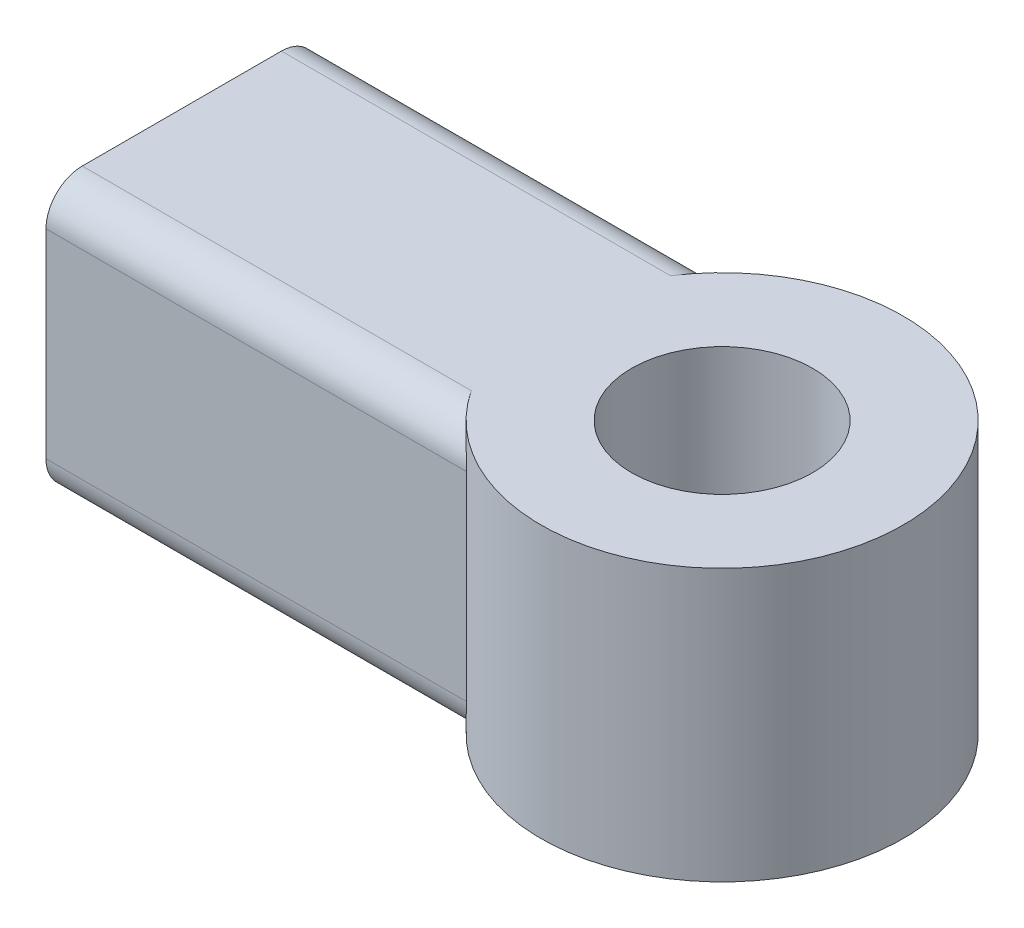
SolidWorks part; units mm, degrees
ref_plane "Front Plane" through (0, 0, 0) normal (0, 0, 1) x (1, 0, 0)
ref_plane "Top Plane" through (0, 0, 0) normal (0, 1, 0) x (1, 0, 0)
ref_plane "Right Plane" through (0, 0, 0) normal (1, 0, 0) x (0, 0, -1)
sketch "Sketch1" plane through (0, 0, 0) normal (0, 1, 0) x (1, 0, 0)
  line L0 (-4.2001, -4.7625) -> (-18.9485, -4.7625)
  line L3 (-4.2001, 4.7625) -> (-18.9485, 4.7625)
  line L4 (-18.9485, -4.7625) -> (-18.9485, 4.7625)
  circle A0 centre (0, 0) radius 3.175
  arc A1 (-4.2001, -4.7625) -> (-4.2001, 4.7625) centre (0, 0) ccw
  dimension "D1" = 6.35
  dimension "D2" = 12.7
extrude "Boss-Extrude1" add sketch "Sketch1" along normal blind 9.525
fillet "Fillet1" radius 1.27 4 edges at (-11.5743, 9.525, -4.7625) (-11.5743, 0, -4.7625) (-11.5743, 0, 4.7625) (-11.5743, 9.525, 4.7625)
sketch "Sketch2" plane through (-18.9485, 0, 0) normal (-1, 0, 0) x (0, 0, 1)
  line L0 (0, 9.525) -> (0, 0) construction
  line L1 (-3.4925, 9.525) -> (3.4925, 9.525) construction
  line L2 (-3.4925, 0) -> (3.4925, 0) construction
  circle A0 centre (0, 4.7625) radius 3.175
  dimension "D1" = 6.35
extrude "Cut-Extrude1" cut sketch "Sketch2" against normal blind 12.7
